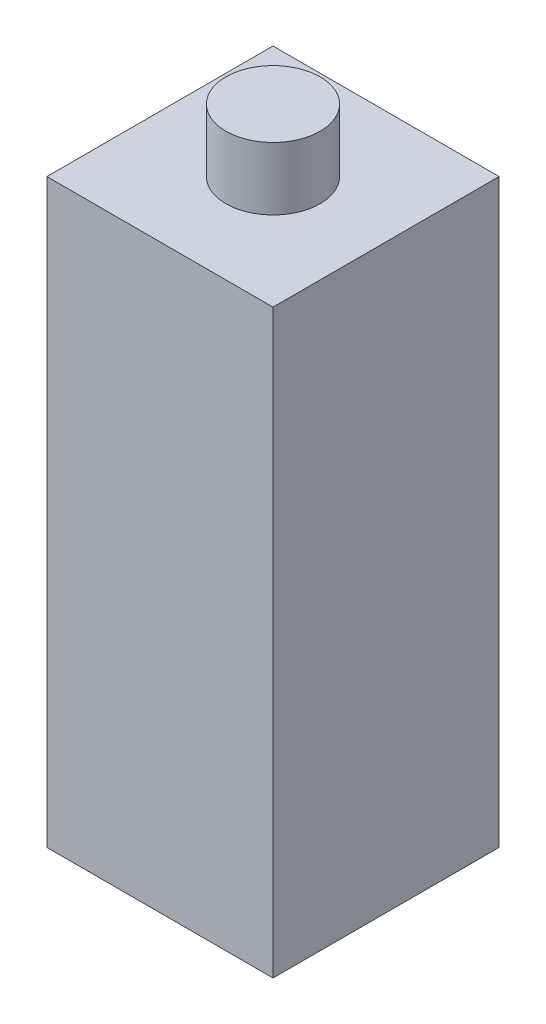
SolidWorks part; units mm, degrees
ref_plane "Front Plane" through (0, 0, 0) normal (0, 0, 1) x (1, 0, 0)
ref_plane "Top Plane" through (0, 0, 0) normal (0, 1, 0) x (1, 0, 0)
ref_plane "Right Plane" through (0, 0, 0) normal (1, 0, 0) x (0, 0, -1)
sketch "Sketch1" plane through (0, 0, 0) normal (0, 1, 0) x (1, 0, 0)
  line L1 (-36, 36) -> (36, 36)
  line L2 (-36, 36) -> (-36, -36)
  line L3 (-36, -36) -> (36, -36)
  line L4 (36, 36) -> (36, -36)
  line L5 (-36, 36) -> (36, -36) construction
  line L6 (-36, -36) -> (36, 36) construction
  point P0 (0, 0)
  dimension "D1" = 72
  dimension "D2" = 72
extrude "Boss-Extrude1" add sketch "Sketch1" along normal blind 185
sketch "Sketch2" plane through (0, 185, 0) normal (0, 1, 0) x (1, 0, 0)
  circle A0 centre (0, 0) radius 15
  dimension "D1" = 30
extrude "Boss-Extrude2" add sketch "Sketch2" along normal blind 20 and the other way blind 205
